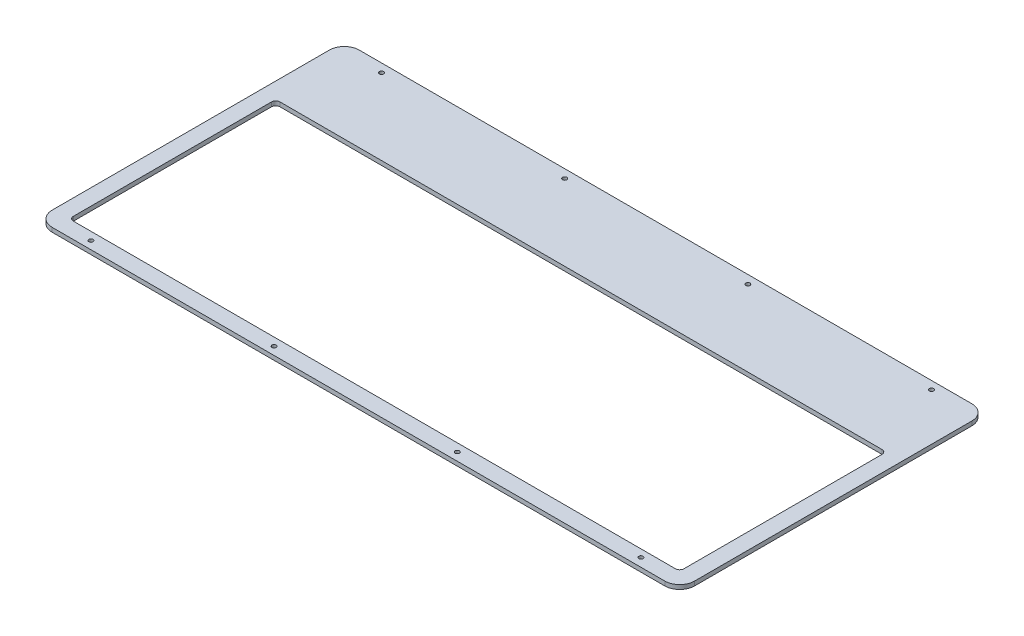
SolidWorks part; units mm, degrees
ref_plane "Front Plane" through (0, 0, 0) normal (0, 0, 1) x (1, 0, 0)
ref_plane "Top Plane" through (0, 0, 0) normal (0, 1, 0) x (1, 0, 0)
ref_plane "Right Plane" through (0, 0, 0) normal (1, 0, 0) x (0, 0, -1)
sketch "Sketch1" plane through (0, 0, 0) normal (0, 1, 0) x (1, 0, 0)
  line L1 (0, 0) -> (350, 0)
  line L2 (0, 0) -> (0, 250)
  line L3 (0, 250) -> (350, 250)
  line L4 (350, 0) -> (350, 250)
extrude "Boss-Extrude1" add sketch "Sketch1" along normal blind 2
sketch "Sketch2" plane through (0, 2, 0) normal (0, 1, 0) x (1, 0, 0)
  line L0 (312.8218, 39.7373) -> (30.1224, 39.7373)
  line L1 (20.6224, 39.2373) -> (20.6224, 169.4368)
  line L2 (315.3218, 32.2373) -> (27.6224, 32.2373)
  line L3 (322.3218, 169.4368) -> (322.3218, 39.2373)
  line L4 (27.6224, 176.4368) -> (315.3218, 176.4368)
  line L5 (28.1224, 41.7373) -> (28.1224, 134.7373)
  line L6 (30.1224, 136.7373) -> (312.8218, 136.7373)
  line L7 (314.8218, 41.7373) -> (314.8218, 134.7373)
  arc A0 (312.8218, 39.7373) -> (314.8218, 41.7373) centre (312.8218, 41.7373) ccw
  arc A1 (28.1224, 41.7373) -> (30.1224, 39.7373) centre (30.1224, 41.7373) ccw
  arc A2 (27.6224, 176.4368) -> (20.6224, 169.4368) centre (27.6224, 169.4368) ccw
  arc A3 (20.6224, 39.2373) -> (27.6224, 32.2373) centre (27.6224, 39.2373) ccw
  arc A4 (315.3218, 32.2373) -> (322.3218, 39.2373) centre (315.3218, 39.2373) ccw
  arc A5 (322.3218, 169.4368) -> (315.3218, 176.4368) centre (315.3218, 169.4368) ccw
  arc A6 (30.1224, 136.7373) -> (28.1224, 134.7373) centre (30.1224, 134.7373) ccw
  arc A7 (314.8218, 134.7373) -> (312.8218, 136.7373) centre (312.8218, 134.7373) ccw
  circle A8 centre (42.1224, 172.4368) radius 1
  circle A9 centre (128.1224, 172.4368) radius 1
  circle A10 centre (214.1224, 172.4368) radius 1
  circle A11 centre (300.1224, 172.6868) radius 1
  circle A12 centre (300.1224, 36.2373) radius 1
  circle A13 centre (214.1224, 35.9873) radius 1
  circle A14 centre (128.1224, 35.9873) radius 1
  circle A15 centre (42.1224, 35.9873) radius 1
extrude "Cut-Extrude1" cut sketch "Sketch2" against normal blind 10 flip side to cut
